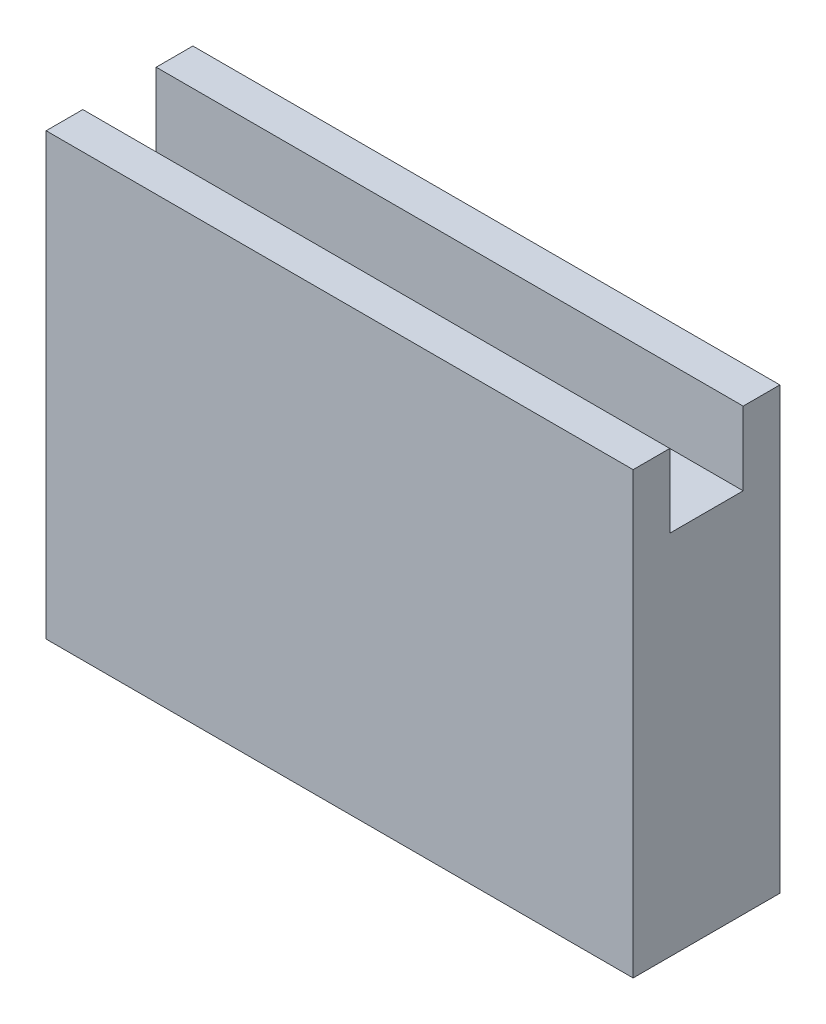
SolidWorks part; units mm, degrees
ref_plane "Front" through (0, 0, 0) normal (0, 0, 1) x (1, 0, 0)
ref_plane "Top" through (0, 0, 0) normal (0, 1, 0) x (1, 0, 0)
ref_plane "Right" through (0, 0, 0) normal (1, 0, 0) x (0, 0, -1)
sketch "Sketch1" plane through (0, 0, 0) normal (0, 1, 0) x (1, 0, 0)
  line L1 (-25.4, -6.35) -> (25.4, -6.35)
  line L2 (-25.4, -6.35) -> (-25.4, 6.35)
  line L3 (-25.4, 6.35) -> (25.4, 6.35)
  line L4 (25.4, -6.35) -> (25.4, 6.35)
  line L5 (-25.4, -6.35) -> (25.4, 6.35) construction
  line L6 (-25.4, 6.35) -> (25.4, -6.35) construction
  point P0 (0, 0)
  dimension "D1" = 50.8
  dimension "D2" = 12.7
extrude "Boss-Extrude1" add sketch "Sketch1" along normal blind 31.75 contours L2 L3 L4 L1
sketch "Sketch2" plane through (0, 31.75, 0) normal (0, 1, 0) x (1, 0, 0)
  line L0 (25.4, -6.35) -> (25.4, 6.35) construction
  line L1 (-25.4, -6.35) -> (25.4, -6.35)
  line L2 (-25.4, -6.35) -> (-25.4, -3.175)
  line L3 (-25.4, -3.175) -> (25.4, -3.175)
  line L4 (25.4, -6.35) -> (25.4, -3.175)
  line L5 (-25.4, -6.35) -> (-25.4, 6.35) construction
  line L6 (25.4, 6.35) -> (-25.4, 6.35)
  line L7 (25.4, 6.35) -> (25.4, 3.175)
  line L8 (25.4, 3.175) -> (-25.4, 3.175)
  line L9 (-25.4, 6.35) -> (-25.4, 3.175)
  dimension "D1" = 3.175
extrude "Boss-Extrude2" add sketch "Sketch2" along normal blind 6.35
